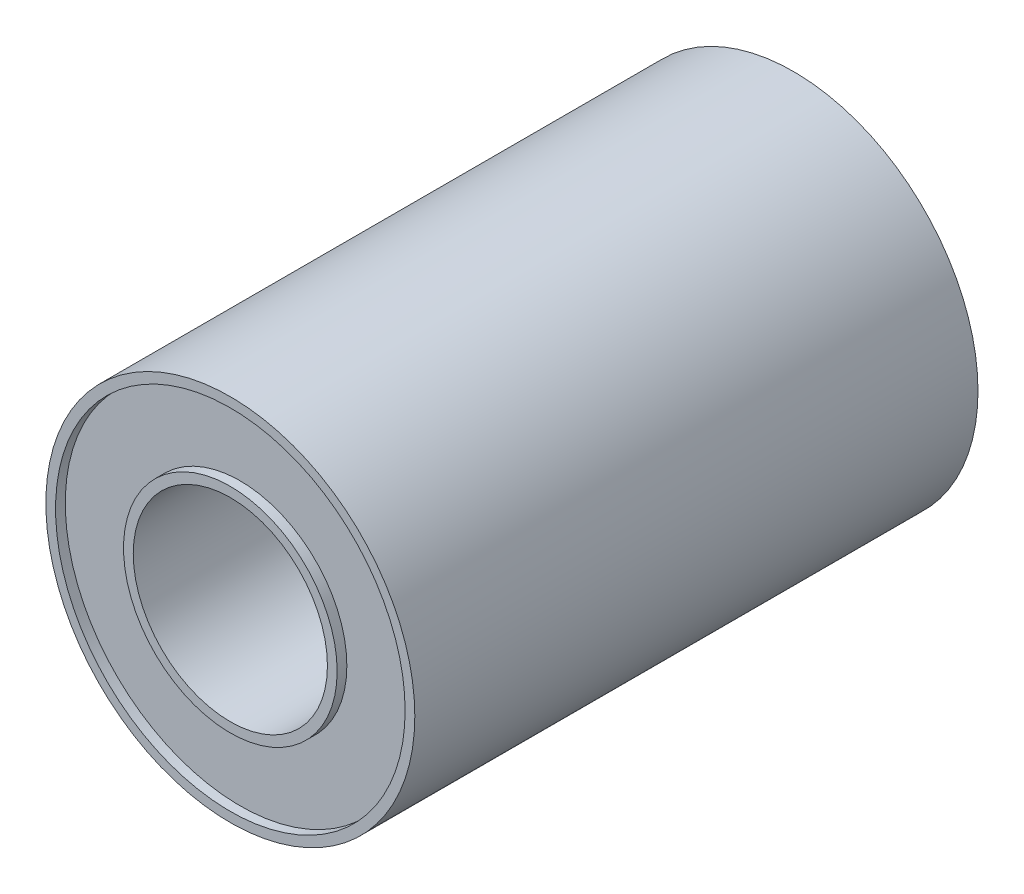
SolidWorks part; units mm, degrees
ref_plane "Ebene vorne" through (0, 0, 0) normal (0, 0, 1) x (1, 0, 0)
ref_plane "Ebene oben" through (0, 0, 0) normal (0, 1, 0) x (1, 0, 0)
ref_plane "Ebene rechts" through (0, 0, 0) normal (1, 0, 0) x (0, 0, -1)
sketch "Skizze1" plane through (0, 0, 0) normal (0, 0, 1) x (1, 0, 0)
  circle A0 centre (0, 0) radius 9.5
  circle A1 centre (0, 0) radius 5
extrude "Aufsatz-Linear austragen1" add sketch "Skizze1" against normal blind 29
sketch "Skizze2" plane through (0, 0, 0) normal (0, 0, 1) x (1, 0, 0)
  circle A0 centre (0, 0) radius 5.5
  circle A1 centre (0, 0) radius 9
extrude "Schnitt-Linear austragen1" cut sketch "Skizze2" against normal blind 0.5
sketch "Skizze3" plane through (0, 0, -29) normal (0, 0, -1) x (-1, 0, 0)
  circle A0 centre (0, 0) radius 5.5
  circle A1 centre (0, 0) radius 9
extrude "Schnitt-Linear austragen2" cut sketch "Skizze3" against normal blind 0.5
